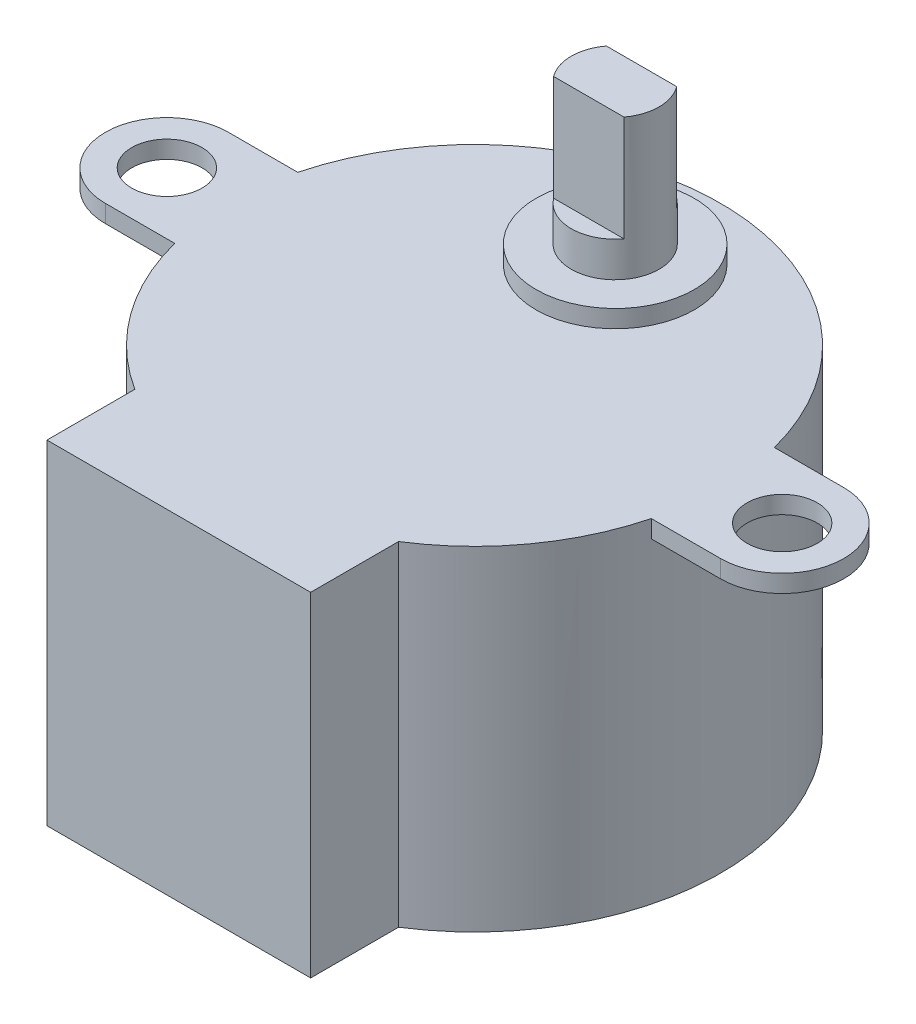
SolidWorks part; units mm, degrees
ref_plane "Front Plane" through (0, 0, 0) normal (0, 0, 1) x (1, 0, 0)
ref_plane "Top Plane" through (0, 0, 0) normal (0, 1, 0) x (1, 0, 0)
ref_plane "Right Plane" through (0, 0, 0) normal (1, 0, 0) x (0, 0, -1)
sketch "Esquisse1" plane through (0, 0, 0) normal (0, 1, 0) x (1, 0, 0)
  line L2 (-7.5, -11.8216) -> (-7.5, -16.8216)
  line L3 (-7.5, -16.8216) -> (7.5, -16.8216)
  line L4 (7.5, -11.8216) -> (7.5, -16.8216)
  arc A0 (7.5, -11.8216) -> (-7.5, -11.8216) centre (0, 0) ccw
  point P1 (0, -16.8216)
  dimension "D1" = 28
  dimension "D2" = 15
  dimension "D3" = 5
extrude "Boss.-Extru.1" add sketch "Esquisse1" along normal blind 19
sketch "Esquisse2" plane through (0, 19, 0) normal (0, 1, 0) x (1, 0, 0)
  line L0 (13.5554, 3.5) -> (17.5, 3.5)
  line L1 (17.5, -3.5) -> (13.5554, -3.5)
  line L2 (0, 2.4016) -> (0, -2.868) construction
  line L3 (-17.5, -3.5) -> (-13.5554, -3.5)
  line L4 (-13.5554, 3.5) -> (-17.5, 3.5)
  arc A0 (13.5554, 3.5) -> (13.5554, -3.5) centre (0, 0) cw
  arc A1 (7.5, -11.8216) -> (-7.5, -11.8216) centre (0, 0) ccw construction
  arc A2 (17.5, 3.5) -> (17.5, -3.5) centre (17.5, 0) cw
  circle A3 centre (17.5, 0) radius 2
  circle A4 centre (-17.5, 0) radius 2
  arc A5 (-17.5, 3.5) -> (-17.5, -3.5) centre (-17.5, 0) ccw
  arc A6 (-13.5554, 3.5) -> (-13.5554, -3.5) centre (0, 0) ccw
  dimension "D1" = 4
  dimension "D2" = 3.5
  dimension "D3" = 35
extrude "Boss.-Extru.2" add sketch "Esquisse2" against normal blind 1
sketch "Esquisse3" plane through (0, 19, 0) normal (0, 1, 0) x (1, 0, 0)
  circle A0 centre (0, 8) radius 4.5
  dimension "D1" = 9
  dimension "D2" = 8
extrude "Boss.-Extru.3" add sketch "Esquisse3" along normal blind 1
sketch "Esquisse4" plane through (0, 20, 0) normal (0, 1, 0) x (1, 0, 0)
  circle A0 centre (0, 8) radius 2.5
  circle A1 centre (0, 8) radius 4.5 construction
  dimension "D1" = 5
extrude "Boss.-Extru.4" add sketch "Esquisse4" along normal blind 8
sketch "Esquisse5" plane through (0, 28, 0) normal (0, 1, 0) x (1, 0, 0)
  line L0 (-2, 9.5) -> (2, 9.5)
  line L1 (-2, 6.5) -> (2, 6.5)
  arc A0 (-2, 9.5) -> (2, 9.5) centre (0, 8) cw
  circle A1 centre (0, 8) radius 2.5 construction
  circle A2 centre (0, 8) radius 2.5 construction
  arc A3 (-2, 6.5) -> (2, 6.5) centre (0, 8) ccw
  arc A4 (-2, 6.5) -> (2, 6.5) centre (0, 8) ccw
  circle M4 centre (0, 8) radius 2.5
  dimension "D1" = 3
extrude "Enlèv. mat.-Extru.1" cut sketch "Esquisse5" against normal blind 6 contours L1 M4 | L0 M4
